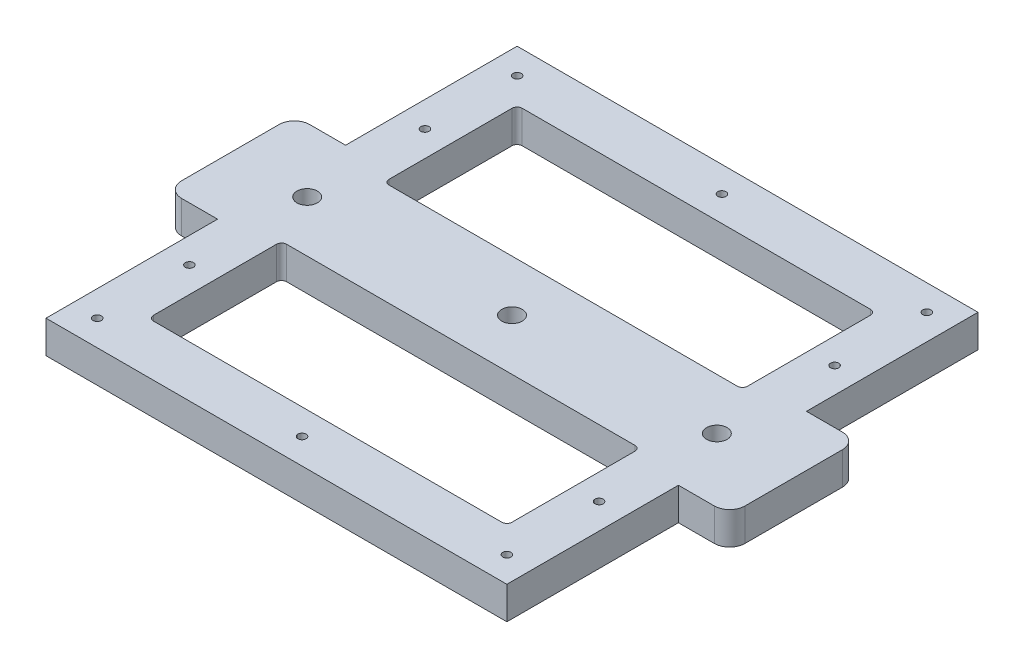
SolidWorks part; units mm, degrees
material "Acrylic (Medium-high impact)"
ref_plane "Front Plane" through (0, 0, 0) normal (0, 0, 1) x (1, 0, 0)
ref_plane "Top Plane" through (0, 0, 0) normal (0, 1, 0) x (1, 0, 0)
ref_plane "Right Plane" through (0, 0, 0) normal (1, 0, 0) x (0, 0, -1)
sketch "Sketch1" plane through (0, 0, 0) normal (0, 1, 0) x (1, 0, 0)
  line L0 (10, 10) -> (0, 0)
  line L1 (0, 0) -> (90, 0)
  line L2 (0, 0) -> (0, 46)
  line L3 (0, 46) -> (90, 46)
  line L4 (90, 0) -> (90, 46)
  line L5 (10, 10) -> (80, 10)
  line L6 (10, 10) -> (10, 36)
  line L7 (10, 36) -> (80, 36)
  line L8 (80, 10) -> (80, 36)
  line L9 (10, 36) -> (0, 46)
  line L10 (80, 36) -> (90, 46)
  line L11 (80, 10) -> (90, 0)
  dimension "D1" = 90
  dimension "D2" = 46
  dimension "D3" = 26
  dimension "D4" = 70
extrude "Boss-Extrude1" add sketch "Sketch1" along normal blind 6.35 contours L6 L9 L2 L0 | L7 L10 L3 L9 | L11 L5 L0 L1 | L8 L11 L4 L10
fillet "Fillet1" radius 1 4 edges at (80, 3.175, -10) (80, 3.175, -36) (10, 3.175, -10) (10, 3.175, -36)
sketch "Sketch2" plane through (0, 6.35, 0) normal (0, 1, 0) x (1, 0, 0)
  line L0 (5, 41) -> (0, 46)
  line L1 (5, 41) -> (85, 41)
  line L2 (5, 41) -> (5, 5)
  line L3 (5, 5) -> (85, 5)
  line L4 (85, 41) -> (85, 5)
  line L5 (85, 41) -> (90, 46)
  line L6 (5, 5) -> (0, 0)
  line L7 (85, 5) -> (90, 0)
  line L8 (5, 41) -> (0, 41)
  line L9 (0, 0) -> (0, 46) construction
  line L10 (5, 41) -> (5, 46)
  line L11 (0, 46) -> (90, 46) construction
  dimension "D1" = 5
hole_wizard "Tap Drill for M2x0.4 Tap1" positions "Sketch3" profile "Sketch5" hole size "M2x0.4" standard "ANSI Metric" end condition through all
sketch "Sketch3" plane through (0, 6.35, 0) normal (0, 1, 0) x (1, 0, 0)
  point P6 (85, 5)
  point P9 (5, 5)
sketch "Sketch5" plane through (85, 6.35, -5) normal (1, 0, 0) x (0, 0, 1)
  line L0 (0, 0) -> (0, 6.35)
  line L1 (0, 6.35) -> (0.8, 6.35)
  line L2 (0.8, 6.35) -> (0.8, 0)
  line L5 (0.8, 0) -> (0, 0)
  line L11 (0, -6.35) -> (0, 107.95) construction
  dimension "Thru Hole Dia." = 1.6
  dimension "Thru Hole Depth" = 6.35
ref_plane "Plane1" through (0, 0, -46) normal (0, 0, -1) x (-1, 0, 0)
sketch "Sketch7" plane through (0, 6.35, 0) normal (0, 1, 0) x (1, 0, 0)
  line L0 (5, 41) -> (85, 41) construction
  line L1 (85, 41) -> (85, 5) construction
  line L2 (85, 5) -> (5, 5) construction
  line L3 (5, 5) -> (5, 41) construction
  circle A1 centre (85, 23) radius 0.8
  circle A2 centre (45, 5) radius 0.8
  circle A3 centre (5, 23) radius 0.8
  circle A4 centre (5, 41) radius 0.8 construction
extrude "Cut-Extrude1" cut sketch "Sketch7" against normal through all
mirror "Mirror1" about plane through (0, 0, -46) normal (0, 0, -1) of "Boss-Extrude1", "Fillet1", "Tap Drill for M2x0.4 Tap1"
sketch "Sketch6" plane through (90, 0, 0) normal (1, 0, 0) x (0, 0, -1)
  line L0 (0, 0) -> (92, 0) construction
  line L1 (33.5, 6.35) -> (58.5, 6.35)
  line L2 (33.5, 6.35) -> (33.5, 0)
  line L3 (33.5, 0) -> (58.5, 0)
  line L4 (58.5, 6.35) -> (58.5, 0)
  line L5 (33.5, 6.35) -> (58.5, 0) construction
  line L6 (33.5, 0) -> (58.5, 6.35) construction
  line L7 (92, 6.35) -> (92, 0) construction
  point P0 (46, 3.175)
  point P8 (46, 6.35)
  dimension "D1" = 25
  dimension "D2" = 6.35
  dimension "D3" = 46
extrude "Boss-Extrude2" add sketch "Sketch6" along normal blind 10
fillet "Fillet2" radius 3 2 edges at (100, 3.175, -58.5) (100, 3.175, -33.5)
ref_plane "Plane2" through (45, 0, 0) normal (-1, 0, 0) x (0, 0, 1)
mirror "Mirror2" about plane through (45, 0, 0) normal (-1, 0, 0) of "Fillet2", "Boss-Extrude2"
mirror "Mirror3" about plane through (0, 0, -46) normal (0, 0, -1) of "Cut-Extrude1"
sketch "Sketch8" plane through (0, 0, 0) normal (0, -1, 0) x (-1, 0, 0)
  line L0 (-5, 23) -> (-5, 69) construction
  line L1 (-85, 23) -> (-85, 69) construction
  line L2 (-85, 46) -> (-5, 46) construction
  circle A0 centre (-45, 46) radius 2
  circle A1 centre (-85, 46) radius 2
  circle A2 centre (-5, 46) radius 2
  dimension "D1" = 4
extrude "Cut-Extrude2" cut sketch "Sketch8" against normal blind 10
equation "\"wall\"=10"
equation "\"D1@Sketch1\"=70+2*\"wall\""
equation "\"D2@Sketch1\"=26+2*\"wall\""
equation "\"thick\"=6.35"
equation "\"D1@Boss-Extrude1\"=\"thick\""
